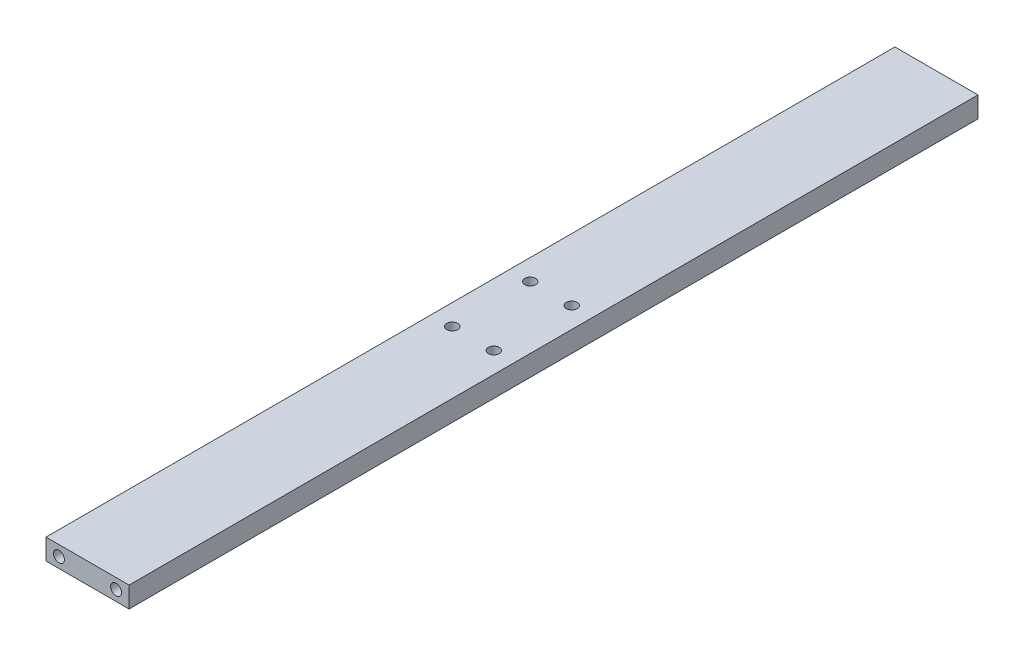
SolidWorks part; units mm, degrees
ref_plane "Front Plane" through (0, 0, 0) normal (0, 0, 1) x (1, 0, 0)
ref_plane "Top Plane" through (0, 0, 0) normal (0, 1, 0) x (1, 0, 0)
ref_plane "Right Plane" through (0, 0, 0) normal (1, 0, 0) x (0, 0, -1)
sketch "Sketch1" plane through (0, 0, 0) normal (0, 0, 1) x (1, 0, 0)
  line L1 (16, -4) -> (-16, -4)
  line L2 (16, -4) -> (16, 4)
  line L3 (16, 4) -> (-16, 4)
  line L4 (-16, -4) -> (-16, 4)
  line L5 (16, -4) -> (-16, 4) construction
  line L6 (16, 4) -> (-16, -4) construction
  point P0 (0, 0)
  dimension "D1" = 8
  dimension "D2" = 32
extrude "Boss-Extrude1" add sketch "Sketch1" along normal mid plane 327
sketch "Sketch2" plane through (0, 0, 163.5) normal (0, 0, 1) x (1, 0, 0)
  circle A0 centre (11, 0) radius 2.1
  circle A2 centre (-11, 0) radius 2.1
extrude "Cut-Extrude1" cut sketch "Sketch2" against normal blind 10
mirror "Mirror1" about plane through (0, 0, 0) normal (0, 0, 1) of "Cut-Extrude1"
sketch "Sketch3" plane through (0, 4, 0) normal (0, 1, 0) x (1, 0, 0)
  circle A0 centre (-8, -15) radius 2.1
  circle A1 centre (-8, 15) radius 2.1
  circle A2 centre (8, -15) radius 2.1
  circle A3 centre (8, 15) radius 2.1
extrude "Cut-Extrude2" cut sketch "Sketch3" against normal up to next
